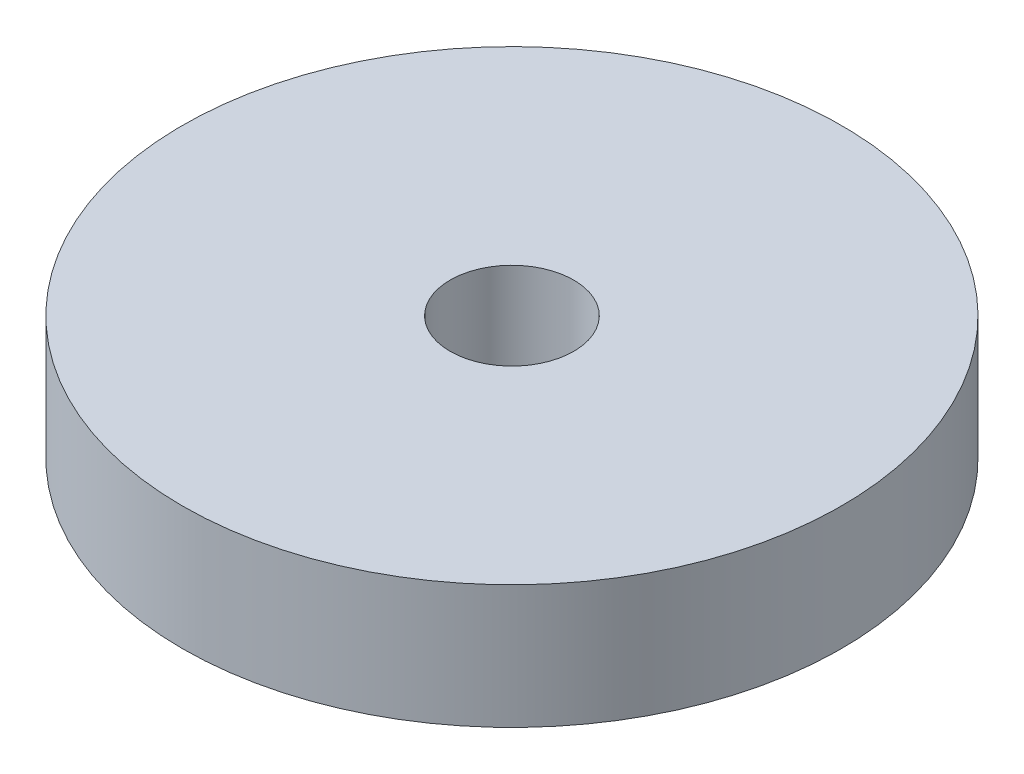
SolidWorks part; units mm, degrees
ref_plane "Front Plane" through (0, 0, 0) normal (0, 0, 1) x (1, 0, 0)
ref_plane "Top Plane" through (0, 0, 0) normal (0, 1, 0) x (1, 0, 0)
ref_plane "Right Plane" through (0, 0, 0) normal (1, 0, 0) x (0, 0, -1)
sketch "Sketch1" plane through (0, 0, 0) normal (0, 1, 0) x (1, 0, 0)
  circle A0 centre (0, 0) radius 25.4
  circle A1 centre (0, 0) radius 4.7625
  dimension "D1" = 50.8
  dimension "D2" = 9.525
extrude "Boss-Extrude1" add sketch "Sketch1" along normal mid plane 9.525
